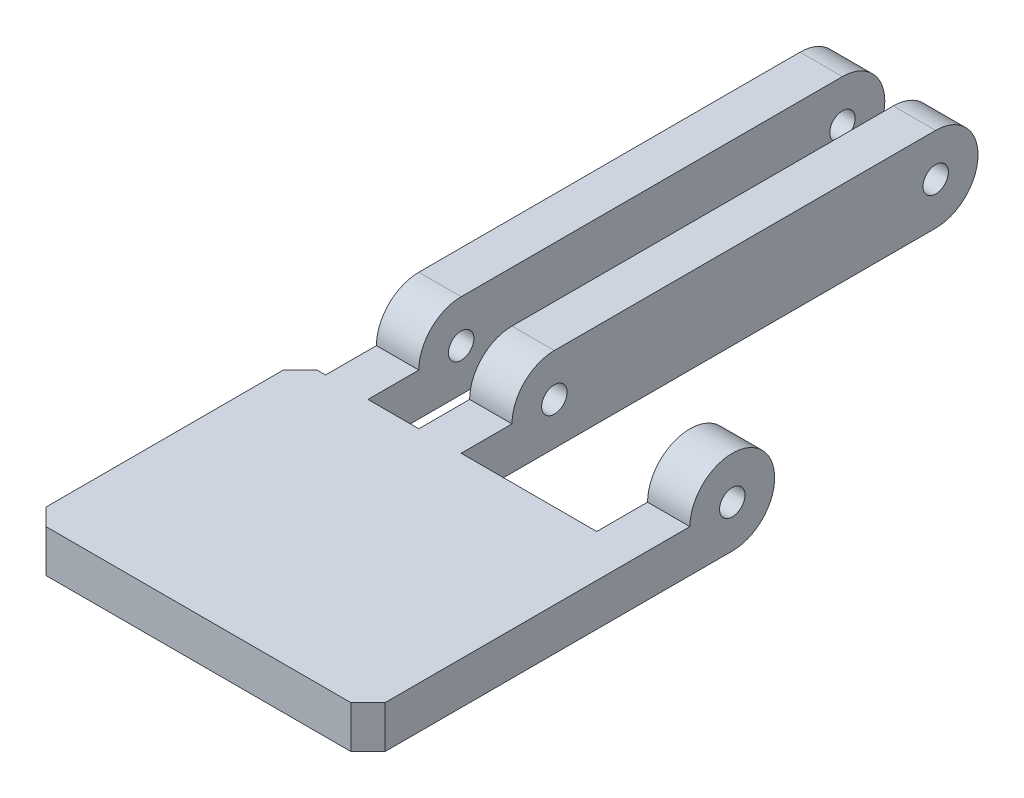
SolidWorks part; units mm, degrees
ref_plane "前视基准面" through (0, 0, 0) normal (0, 0, 1) x (1, 0, 0)
ref_plane "上视基准面" through (0, 0, 0) normal (0, 1, 0) x (1, 0, 0)
ref_plane "右视基准面" through (0, 0, 0) normal (1, 0, 0) x (0, 0, -1)
other "Configuration Table"
sketch "草图1" plane through (0, 0, 0) normal (0, 1, 0) x (1, 0, 0)
  line L0 (0, 0) -> (0, -35.8643) construction
  line L1 (-25, 18) -> (25, 18)
  line L2 (-25, 18) -> (-25, -25)
  line L3 (-25, -25) -> (25, -25)
  line L4 (25, 18) -> (25, -25)
  line L5 (0, 0) -> (25, -25) construction
  line L6 (-25, -25) -> (0, 0) construction
  point P0 (0, 0)
  dimension "D1" = 50
  dimension "D2" = 25
  dimension "D3" = 18
  dimension "D4" = 90
extrude "凸台-拉伸1" add sketch "草图1" along normal blind 5
ref_plane "基准面1" through (15, 0, 0) normal (1, 0, 0) x (0, 0, -1)
sketch "草图3" plane through (15, 0, 0) normal (1, 0, 0) x (0, 0, -1)
  line L0 (18, 5) -> (-7.9808, 20) construction
  line L1 (15.5, 0.6699) -> (-10.4808, 15.6699) construction
  line L2 (20.5, 9.3301) -> (-5.4808, 24.3301) construction
  line L3 (18, 5) -> (-25, 5) construction
  line L4 (18, 5) -> (18, 0) construction
  arc A0 (15.5, 0.6699) -> (20.5, 9.3301) centre (18, 5) ccw construction
  arc A1 (-5.4808, 24.3301) -> (-10.4808, 15.6699) centre (-7.9808, 20) ccw construction
  circle A2 centre (18, 5) radius 5
  point P2 (5.0096, 12.5)
  dimension "D4" = 5
  dimension "D2" = 5
  dimension "D3" = 30
  dimension "D5" = 30
extrude "凸台-拉伸2" add sketch "草图3" against normal blind 5
sketch "草图5" plane through (0, 0, 0) normal (1, 0, 0) x (0, 0, -1)
  line L0 (18, 5) -> (63, 5) construction
  line L1 (18, 10) -> (63, 10)
  line L2 (18, 0) -> (63, 0)
  arc A1 (18, 0) -> (20.5, 9.3301) centre (18, 5) ccw
  circle A2 centre (18, 5) radius 5
  arc A4 (18, 0) -> (13, 5) centre (18, 5) ccw construction
  arc A5 (18, 10) -> (18, 0) centre (18, 5) ccw
  arc A6 (63, 0) -> (63, 10) centre (63, 5) ccw
  point P7 (40.5, 5)
  dimension "D1" = 45
extrude "凸台-拉伸3" add sketch "草图5" against normal blind 5 from offset 6 contours L2 A6 L1 A5 offset against normal yes
ref_plane "基准面2" through (-22, 0, 0) normal (1, 0, 0) x (0, 0, -1)
sketch "草图6" plane through (-22, 0, 0) normal (1, 0, 0) x (0, 0, -1)
  line L0 (18, 5) -> (63, 5) construction
  line L1 (18, 10) -> (63, 10)
  line L2 (18, 0) -> (63, 0)
  circle A0 centre (18, 5) radius 5
  arc A2 (18, 10) -> (13, 5) centre (18, 5) ccw construction
  arc A3 (18, 10) -> (18, 0) centre (18, 5) ccw
  arc A4 (63, 0) -> (63, 10) centre (63, 5) ccw
  point P6 (40.5, 5)
extrude "凸台-拉伸4" add sketch "草图6" along normal blind 5
sketch "草图9" plane through (15, 0, 0) normal (1, 0, 0) x (0, 0, -1)
  circle A0 centre (18, 5) radius 1.5
  arc A1 (18, 0) -> (13, 5) centre (18, 5) ccw construction
  point P3 (0, 0)
  dimension "D1" = 3
extrude "切除-拉伸2" cut sketch "草图9" against normal through all both and the other way through all
sketch "草图11" plane through (0, 5, 0) normal (0, 1, 0) x (1, 0, 0)
  line L0 (-22, -5.5) -> (-22, 5.5) construction
  line L1 (-25, 18) -> (-22, 18)
  line L2 (-25, 18) -> (-25, 7)
  line L3 (-25, 7) -> (-22, 7)
  line L4 (-22, 18) -> (-22, 7)
  line L5 (15, 16.5) -> (15, 19.5) construction
  line L6 (-17, 18) -> (-11, 18)
  line L7 (-17, 18) -> (-17, 7)
  line L8 (-17, 7) -> (-11, 7)
  line L9 (-11, 18) -> (-11, 7)
  line L10 (-6, 18) -> (10, 18)
  line L11 (-6, 18) -> (-6, 7)
  line L12 (-6, 7) -> (10, 7)
  line L13 (10, 18) -> (10, 7)
  line L14 (15, 18) -> (25, 18)
  line L15 (15, 18) -> (15, 7)
  line L16 (15, 7) -> (25, 7)
  line L17 (25, 18) -> (25, 7)
  line L18 (25, -25) -> (25, 16.5) construction
  line L19 (-11, 18) -> (-11, 13) construction
  line L20 (10, 23) -> (10, 13) construction
  dimension "D1" = 11
extrude "切除-拉伸3" cut sketch "草图11" against normal through all both and the other way through all
sketch "草图12" plane through (-6, 0, 0) normal (1, 0, 0) x (0, 0, -1)
  circle A0 centre (63, 5) radius 1.5
  dimension "D1" = 3
extrude "切除-拉伸4" cut sketch "草图12" against normal through all both and the other way through all
sketch "草图13" plane through (0, 5, 0) normal (0, 1, 0) x (1, 0, 0)
  line L1 (15, 7) -> (25, 7)
  line L2 (15, 7) -> (15, -25)
  line L3 (15, -25) -> (25, -25)
  line L4 (25, 7) -> (25, -25)
extrude "切除-拉伸5" cut sketch "草图13" against normal through all both and the other way through all
chamfer "倒角2" distance 2 angle 45 3 edges at (-25, 2.5, -7) (15, 2.5, 25) (-25, 2.5, 25)
